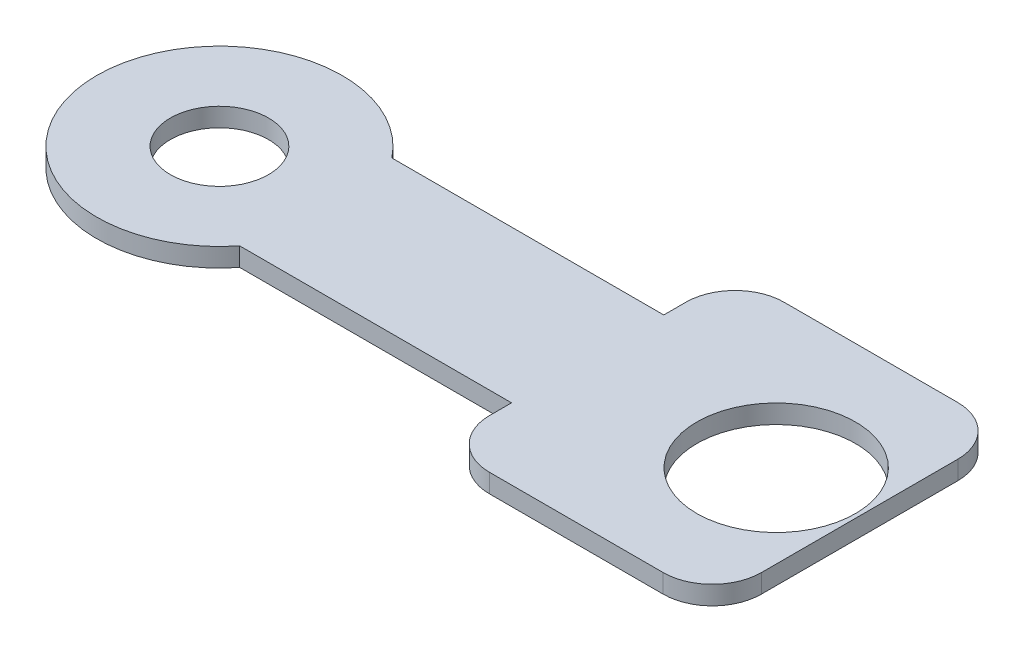
SolidWorks part; units mm, degrees
ref_plane "Front Plane" through (0, 0, 0) normal (0, 0, 1) x (1, 0, 0)
ref_plane "Top Plane" through (0, 0, 0) normal (0, 1, 0) x (1, 0, 0)
ref_plane "Right Plane" through (0, 0, 0) normal (1, 0, 0) x (0, 0, -1)
sketch "Sketch1" plane through (0, 0, 0) normal (0, 1, 0) x (1, 0, 0)
  line L0 (0, 0) -> (10, 0) construction
  line L1 (0, 0) -> (2.5, 0) construction
  line L2 (10, 1.55) -> (4.4615, 1.55)
  line L3 (10, -1.55) -> (4.4615, -1.55)
  line L4 (10, -1.55) -> (10, 1.55) construction
  line L5 (10, 0) -> (15.5385, 0) construction
  line L6 (10, -2) -> (10, 2)
  line L7 (15.5385, -2) -> (15.5385, 2)
  line L9 (11, -3) -> (14.5385, -3)
  line L10 (10, -3) -> (10, 3) construction
  line L11 (11, 3) -> (14.5385, 3)
  line L12 (15.5385, -3) -> (15.5385, 3) construction
  line L17 (12.5897, -1) -> (15.0897, 1) construction
  line L18 (12.5897, 1) -> (15.0897, -1) construction
  circle A0 centre (2.5, 0) radius 2.5 construction
  arc A1 (4.4615, 1.55) -> (4.4651, -1.5454) centre (2.5, 0) ccw
  arc A2 (15.5385, 2) -> (14.5385, 3) centre (14.5385, 2) ccw
  arc A3 (15.5385, -2) -> (14.5385, -3) centre (14.5385, -2) cw
  arc A4 (10, -2) -> (11, -3) centre (11, -2) ccw
  arc A5 (10, 2) -> (11, 3) centre (11, 2) cw
  circle A6 centre (2.5, 0) radius 1
  circle A7 centre (13.8397, 0) radius 1.6164
  point P12 (10, 0)
  point P15 (10, 0)
  point P18 (15.5385, 0)
  point P30 (13.8397, 0)
  dimension "D3" = 6
  dimension "D5" = 1
  dimension "D9" = 2
  dimension "D1" = 10
  dimension "D2" = 2.5
  dimension "D4" = 3.1
  dimension "D6" = 2
  dimension "D7" = 2.5
extrude "Boss-Extrude4" add sketch "Sketch1" along normal blind 0.381
